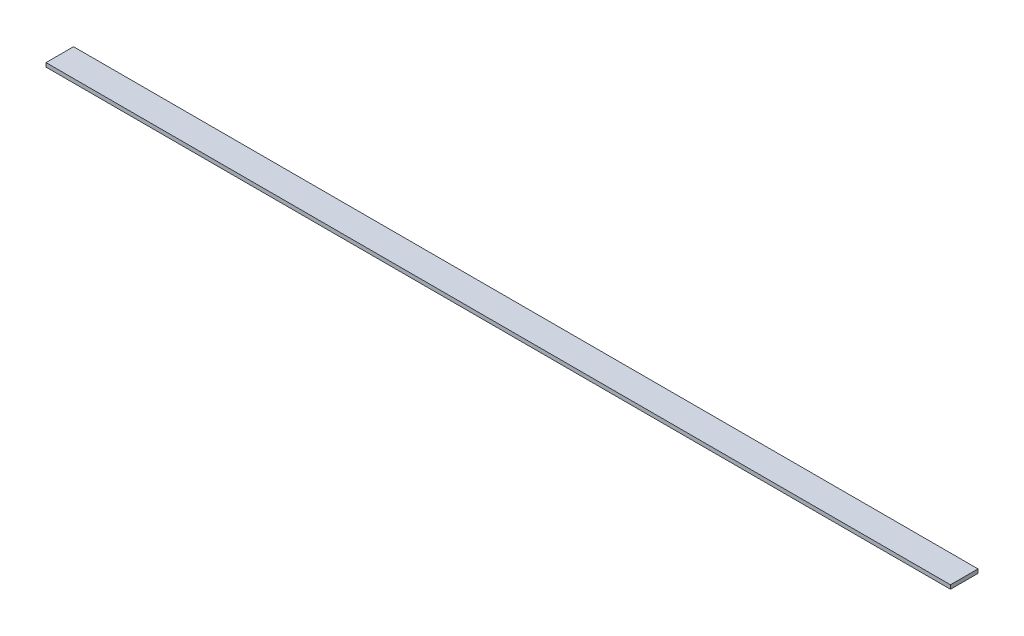
SolidWorks part; units mm, degrees
ref_plane "Front Plane" through (0, 0, 0) normal (0, 0, 1) x (1, 0, 0)
ref_plane "Top Plane" through (0, 0, 0) normal (0, 1, 0) x (1, 0, 0)
ref_plane "Right Plane" through (0, 0, 0) normal (1, 0, 0) x (0, 0, -1)
sketch "Sketch1" plane through (0, 0, 0) normal (0, 1, 0) x (1, 0, 0)
  line L1 (-109.4223, 29.6424) -> (2811.5777, 29.6424)
  line L2 (-109.4223, 29.6424) -> (-109.4223, -59.2576)
  line L3 (-109.4223, -59.2576) -> (2811.5777, -59.2576)
  line L4 (2811.5777, 29.6424) -> (2811.5777, -59.2576)
  dimension "D1" = 2921
  dimension "D2" = 88.9
extrude "Boss-Extrude1" add sketch "Sketch1" along normal blind 12.7
